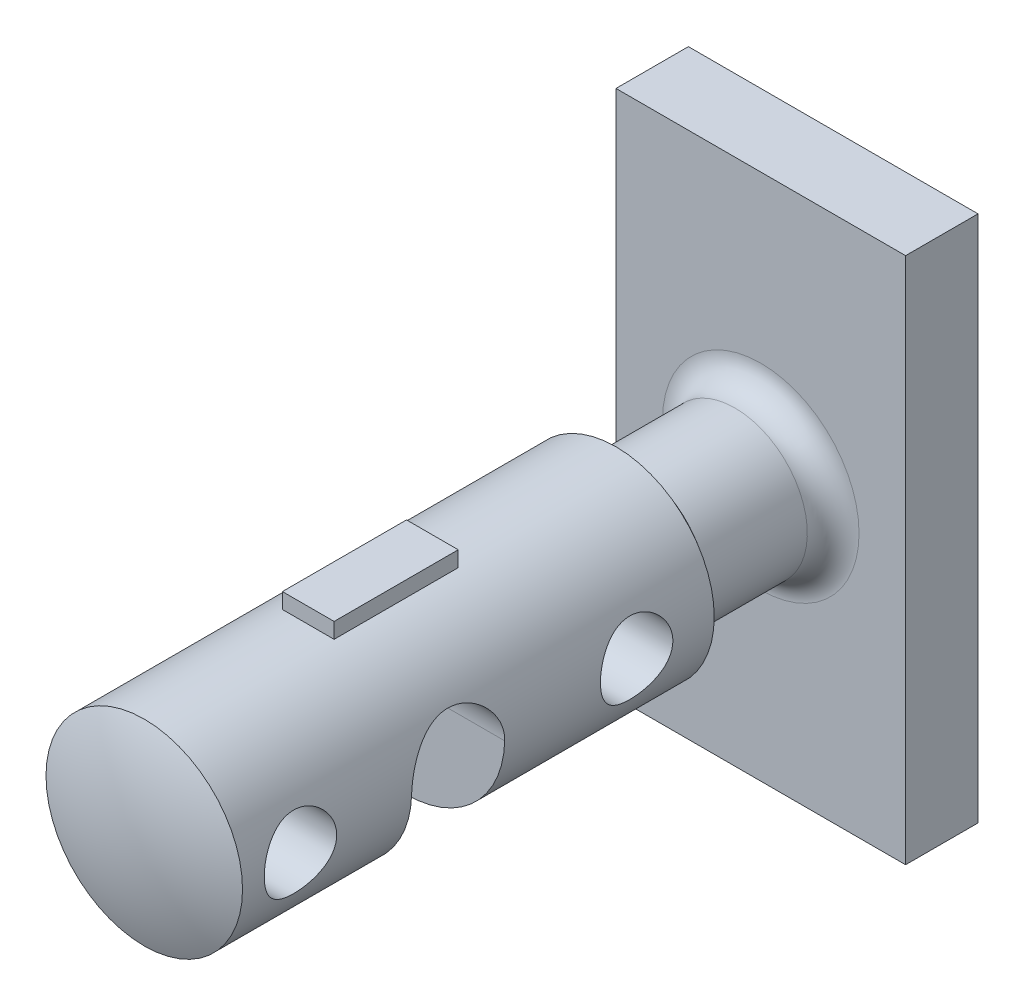
SolidWorks part; units mm, degrees
ref_plane "Front Plane" through (0, 0, 0) normal (0, 0, 1) x (1, 0, 0)
ref_plane "Top Plane" through (0, 0, 0) normal (0, 1, 0) x (1, 0, 0)
ref_plane "Right Plane" through (0, 0, 0) normal (1, 0, 0) x (0, 0, -1)
sketch "Sketch2" plane through (0, 0, 0) normal (0, 1, 0) x (1, 0, 0)
  line L1 (-56, 28) -> (56, 28)
  line L2 (-56, 28) -> (-56, 0)
  line L3 (-56, 0) -> (56, 0)
  line L4 (56, 28) -> (56, 0)
  dimension "D1" = 0
  dimension "D2" = 28
  dimension "D3" = 112
  dimension "D4" = 56
extrude "Boss-Extrude1" add sketch "Sketch2" along normal mid plane 204
sketch "Sketch6" plane through (0, 0, 0) normal (1, 0, 0) x (0, 0, -1)
  line L0 (0, -28) -> (-48.8045, -28)
  line L1 (-48.8045, -28) -> (-56, -38)
  line L2 (-238.4138, -38) -> (-56, -38)
  line L3 (0, -28) -> (0, 0)
  line L4 (0, 0) -> (-147.0345, 0) construction
  line L6 (0, 0) -> (-147.0345, 0)
  line L8 (-147.0345, 0) -> (-246, 0)
  arc A1 (-246, 0) -> (-238.4138, -38) centre (-147.0345, 0) ccw
  dimension "D6" = 98.9655
  dimension "D1" = 56
  dimension "D2" = 38
  dimension "D3" = 28
  dimension "D4" = 76.8045
  dimension "D5" = 190
revolve "Revolve2" add sketch "Sketch6" angle 360 about L4
sketch "Sketch7" plane through (0, 0, 0) normal (1, 0, 0) x (0, 0, -1)
  circle A0 centre (-216, 0) radius 14
  circle A1 centre (-86, 0) radius 14
extrude "Cut-Extrude1" cut sketch "Sketch7" against normal mid plane 204
sketch "Sketch8" plane through (0, 0, 0) normal (1, 0, 0) x (0, 0, -1)
  line L0 (-175, 38) -> (-175, 44)
  line L1 (-56, 38) -> (-246, 38) construction
  line L2 (-175, 44) -> (-127, 44)
  line L3 (-127, 44) -> (-127, 38)
  line L4 (-216, 0) -> (-86, 0) construction
  line L5 (-175, 38) -> (-127, 38)
  point P8 (-151, 0)
  dimension "D1" = 24
  dimension "D2" = 48
  dimension "D3" = 44
extrude "Boss-Extrude3" add sketch "Sketch8" along normal mid plane 20 separate body contours L2 L3 L5 L0
sketch "Sketch11" plane through (0, 0, 0) normal (1, 0, 0) x (0, 0, -1)
  line L0 (-246, -38) -> (-56, -38) construction
  line L1 (-173.0064, -1) -> (-173.0064, -59.7038)
  line L2 (-173.0064, -59.7038) -> (-137.0064, -59.7038)
  line L3 (-137.0064, -59.7038) -> (-137.0064, -1)
  arc A0 (-137.0064, -1) -> (-173.0064, -1) centre (-155.0064, -1) ccw
  dimension "D2" = 36
  dimension "D1" = 37
extrude "Cut-Extrude2" cut sketch "Sketch11" against normal mid plane 124
fillet "Fillet5" radius 10 1 edges at (-28, 0, 0)
